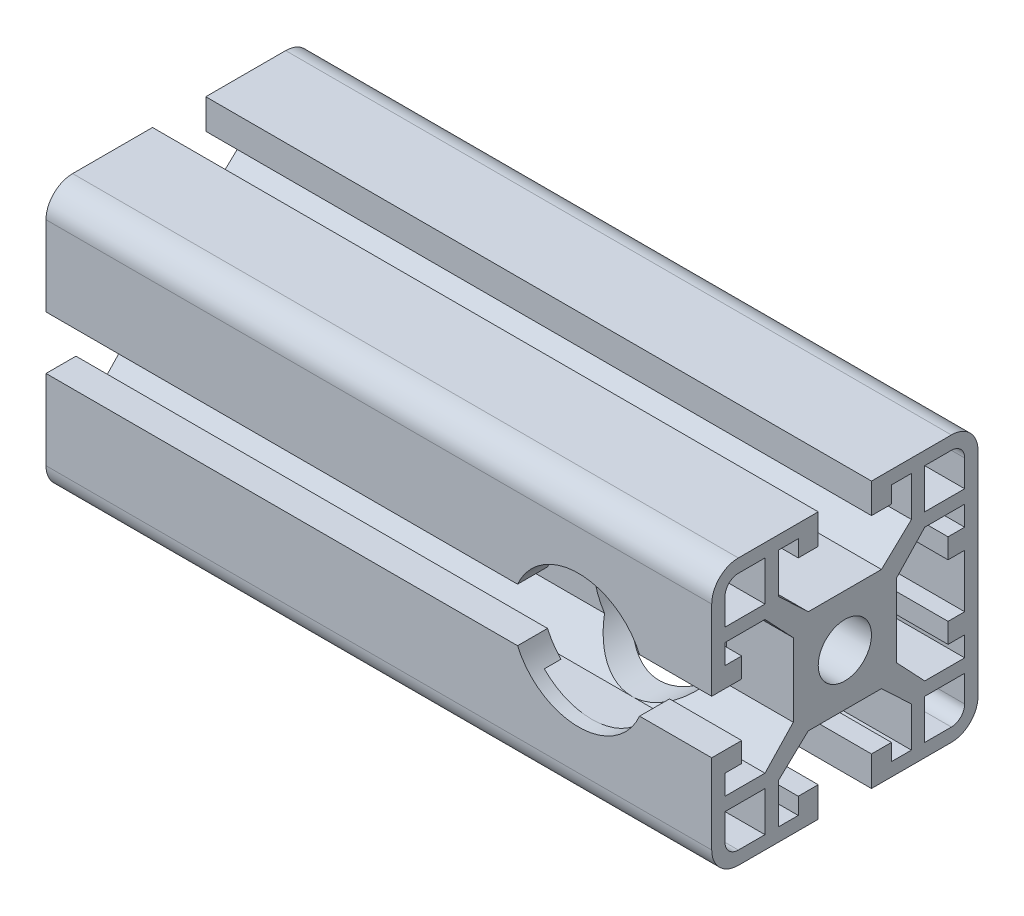
SolidWorks part; units mm, degrees
ref_plane "Oben" through (0, 0, 0) normal (0, 0, 1) x (1, 0, 0)
ref_plane "Front" through (0, 0, 0) normal (0, 1, 0) x (1, 0, 0)
ref_plane "Seite" through (0, 0, 0) normal (1, 0, 0) x (0, 0, -1)
sketch "Skizze1" plane through (0, 0, 0) normal (0, 0, 1) x (1, 0, 0)
  line L0 (100, 0) -> (0, 0)
  dimension "D1" = 100
other "Strukturbauteil1"
ref_plane "Ebene1" through (100, 0, 0) normal (-1, 0, 0) x (0, -1, 0)
sketch "Skizze11" plane through (100, 0, 0) normal (-1, 0, 0) x (0, -1, 0)
  line L0 (12, 18) -> (12, 12)
  line L1 (12, 12) -> (18, 12)
  line L2 (18, 12) -> (18, 16)
  line L3 (16, 18) -> (12, 18)
  line L4 (-18, 12) -> (-12, 12)
  line L5 (-12, 12) -> (-12, 18)
  line L6 (-12, 18) -> (-16, 18)
  line L7 (-18, 16) -> (-18, 12)
  line L8 (16, 20) -> (4, 20)
  line L9 (20, -4) -> (15.5, -4)
  line L10 (18, 10) -> (18, 7)
  line L11 (7.75, 5.5) -> (12, 10)
  line L12 (7.75, 5.5) -> (7.75, -5.5)
  line L13 (12, 10) -> (18, 10)
  line L14 (18, 7) -> (15.5, 7)
  line L15 (18, -10) -> (18, -7)
  line L16 (-20, 16) -> (-20, 4)
  line L17 (-16, -20) -> (16, -20)
  line L18 (-4, -18) -> (4, -18)
  line L29 (15.5, -4) -> (15.5, -7)
  line L30 (18, -10) -> (12, -10)
  line L33 (4, 20) -> (4, 15.5)
  line L34 (-10, 18) -> (-7, 18)
  line L35 (-5.5, 7.75) -> (-10, 12)
  line L36 (-5.5, 7.75) -> (5.5, 7.75)
  line L37 (-10, 12) -> (-10, 18)
  line L38 (-7, 18) -> (-7, 15.5)
  line L39 (10, 18) -> (7, 18)
  line L40 (4, 15.5) -> (7, 15.5)
  line L41 (10, 18) -> (10, 12)
  line L42 (-4, 15.5) -> (-4, 20)
  line L43 (15.5, 4) -> (20, 4)
  line L44 (15.5, 7) -> (15.5, 4)
  line L45 (15.5, -7) -> (18, -7)
  line L46 (-7, 15.5) -> (-4, 15.5)
  line L47 (7, 15.5) -> (7, 18)
  line L48 (10, 12) -> (5.5, 7.75)
  line L49 (12, -10) -> (7.75, -5.5)
  line L50 (20, 4) -> (20, 16)
  line L51 (18, -12) -> (12, -12)
  line L52 (12, -12) -> (12, -18)
  line L53 (12, -18) -> (16, -18)
  line L54 (18, -16) -> (18, -12)
  line L55 (20, -16) -> (20, -4)
  line L56 (-4, -18) -> (-4, -15.5)
  line L57 (10, -18) -> (7, -18)
  line L58 (5.5, -7.75) -> (10, -12)
  line L59 (5.5, -7.75) -> (-5.5, -7.75)
  line L60 (10, -12) -> (10, -18)
  line L61 (7, -18) -> (7, -15.5)
  line L62 (-10, -18) -> (-7, -18)
  line L63 (-4, -15.5) -> (-7, -15.5)
  line L64 (-10, -18) -> (-10, -12)
  line L65 (4, -15.5) -> (4, -18)
  line L66 (7, -15.5) -> (4, -15.5)
  line L67 (-7, -15.5) -> (-7, -18)
  line L68 (-10, -12) -> (-5.5, -7.75)
  line L70 (-12, -18) -> (-12, -12)
  line L71 (-4, 20) -> (-16, 20)
  line L72 (-12, -12) -> (-18, -12)
  line L73 (-18, -12) -> (-18, -16)
  line L74 (-16, -18) -> (-12, -18)
  line L76 (-20, 4) -> (-15.5, 4)
  line L77 (-18, -10) -> (-18, -7)
  line L78 (-7.75, -5.5) -> (-12, -10)
  line L79 (-7.75, -5.5) -> (-7.75, 5.5)
  line L80 (-12, -10) -> (-18, -10)
  line L81 (-18, -7) -> (-15.5, -7)
  line L82 (-18, 10) -> (-18, 7)
  line L83 (-15.5, 4) -> (-15.5, 7)
  line L84 (-18, 10) -> (-12, 10)
  line L85 (-15.5, -4) -> (-20, -4)
  line L86 (-15.5, -7) -> (-15.5, -4)
  line L87 (-15.5, 7) -> (-18, 7)
  line L88 (-12, 10) -> (-7.75, 5.5)
  line L89 (-20, -4) -> (-20, -16)
  arc A0 (18, 16) -> (16, 18) centre (16, 16) ccw
  arc A1 (20, 16) -> (16, 20) centre (16, 16) ccw
  arc A2 (16, -18) -> (18, -16) centre (16, -16) ccw
  arc A3 (16, -20) -> (20, -16) centre (16, -16) ccw
  circle A4 centre (0, 0) radius 4
  arc A5 (-16, 18) -> (-18, 16) centre (-16, 16) ccw
  arc A6 (-18, -16) -> (-16, -18) centre (-16, -16) ccw
  arc A7 (-20, -16) -> (-16, -20) centre (-16, -16) ccw
  arc A76 (-16, 20) -> (-20, 16) centre (-16, 16) ccw
  point P2 (20, 20)
  point P4 (0, 20)
  point P5 (-20, 20)
  point P14 (20, 0)
  point P18 (0, 0)
  point P62 (-20, 0)
  point P67 (-20, -20)
  point P90 (0, -20)
  point P103 (20, -20)
sketch "Skizze2" plane through (60.207, 21.4462, 20) normal (0, 0, 1) x (1, 0, 0)
  line L1 (-60.207, -41.4462) -> (39.793, -41.4462) construction
  line L2 (39.793, -37.4462) -> (39.793, -25.4462) construction
  line L4 (19.793, -21.4462) -> (39.793, -21.4462) construction
  line L11 (19.793, -21.4462) -> (19.793, -41.4462) construction
  circle A0 centre (19.793, -21.4462) radius 10
  point P0 (19.793, -21.4462)
  dimension "Bohrungsdurmesser" = 20
  dimension "Kante_Front" = 20
  dimension "Kante_Position" = 20
extrude "Schnitt-Linear austragen" cut sketch "Skizze2" against normal blind 15.9
other "BohrungitemUni-Verbinder2<1>"
